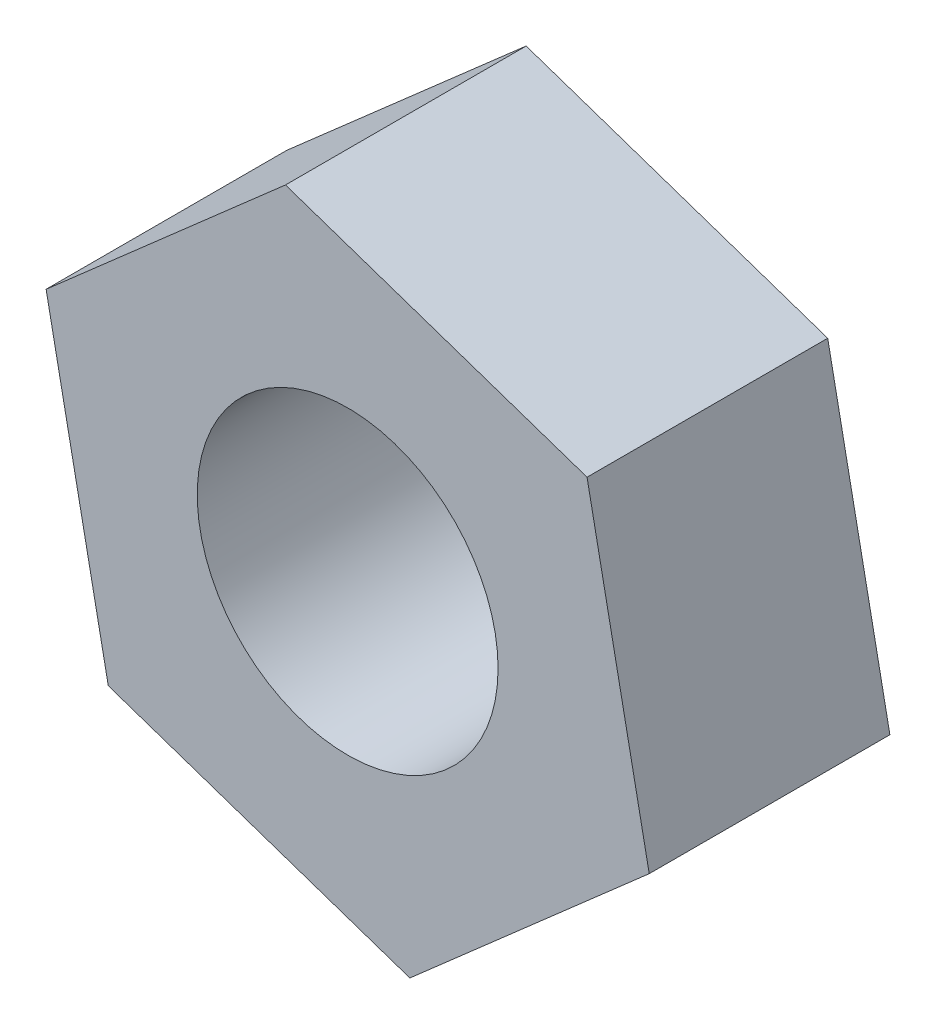
SolidWorks part; units mm, degrees
ref_plane "前视基准面" through (0, 0, 0) normal (0, 0, 1) x (1, 0, 0)
ref_plane "上视基准面" through (0, 0, 0) normal (0, 1, 0) x (1, 0, 0)
ref_plane "右视基准面" through (0, 0, 0) normal (1, 0, 0) x (0, 0, -1)
sketch "草图1" plane through (0, 0, 0) normal (0, 0, 1) x (1, 0, 0)
  line L1 (3.0071, -1.0201) -> (2.387, 2.0942)
  line L2 (2.387, 2.0942) -> (-0.6201, 3.1143)
  line L3 (-0.6201, 3.1143) -> (-3.0071, 1.0201)
  line L4 (-3.0071, 1.0201) -> (-2.387, -2.0942)
  line L5 (-2.387, -2.0942) -> (0.6201, -3.1143)
  line L6 (0.6201, -3.1143) -> (3.0071, -1.0201)
  circle A0 centre (0, 0) radius 2.75 construction
  circle A1 centre (0, 0) radius 1.5
  dimension "D2" = 3
  dimension "D1" = 5.5
extrude "凸台-拉伸1" add sketch "草图1" along normal blind 2.4
